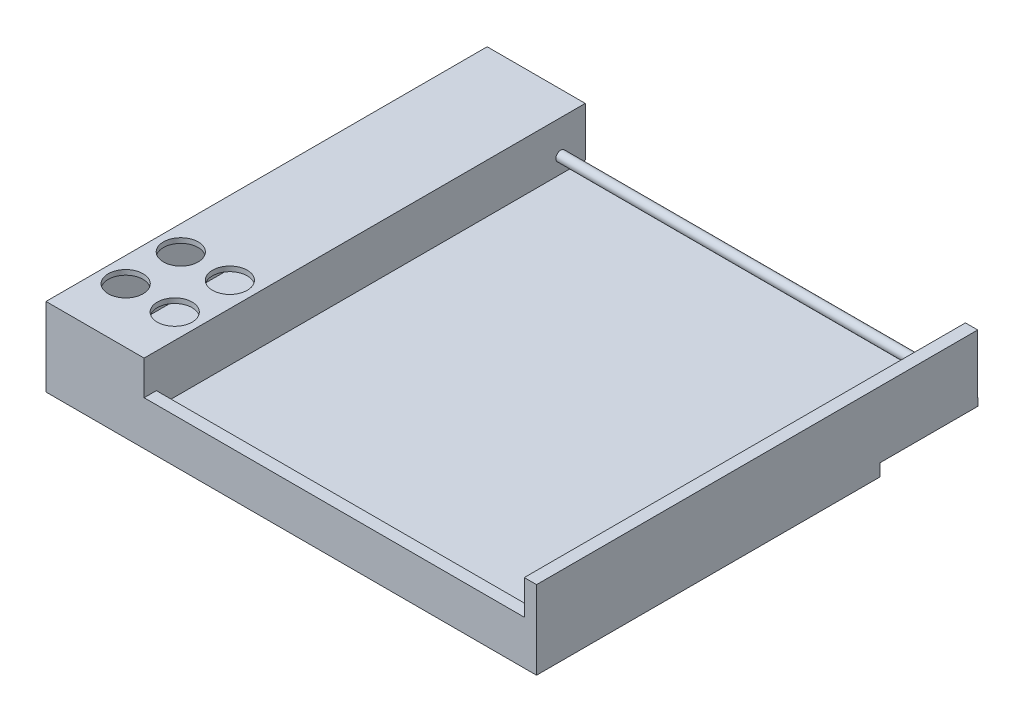
SolidWorks part; units mm, degrees
ref_plane "Front Plane" through (0, 0, 0) normal (0, 0, 1) x (1, 0, 0)
ref_plane "Top Plane" through (0, 0, 0) normal (0, 1, 0) x (1, 0, 0)
ref_plane "Right Plane" through (0, 0, 0) normal (1, 0, 0) x (0, 0, -1)
sketch "Sketch1" plane through (0, 0, 0) normal (0, 1, 0) x (1, 0, 0)
  line L1 (-100, -90) -> (100, -90)
  line L2 (-100, -90) -> (-100, 90)
  line L3 (-100, 90) -> (100, 90)
  line L4 (100, -90) -> (100, 90)
  line L5 (-100, -90) -> (100, 90) construction
  line L6 (-100, 90) -> (100, -90) construction
  point P0 (0, 0)
  dimension "D1" = 200
  dimension "D2" = 180
extrude "Boss-Extrude1" add sketch "Sketch1" along normal blind 3
sketch "Sketch2" plane through (0, 0, 0) normal (0, -1, 0) x (1, 0, 0)
  line L0 (-100, 90) -> (100, 90)
  line L1 (-100, 90) -> (-100, -50)
  line L2 (100, 90) -> (100, -50)
  line L3 (-100, -50) -> (100, -50)
  dimension "D1" = 140
extrude "Boss-Extrude2" add sketch "Sketch2" along normal blind 5
sketch "Sketch6" plane through (0, 3, 0) normal (0, 1, 0) x (1, 0, 0)
  line L0 (-100, -90) -> (100, -90)
  line L1 (-100, -90) -> (-100, 89.8697)
  line L2 (100, -90) -> (100, 89.8697)
  line L3 (-100, 89.8697) -> (100, 89.8697)
extrude "Boss-Extrude3" add sketch "Sketch6" along normal blind 24
sketch "Sketch7" plane through (0, 0, -89.8697) normal (0, 0, -1) x (-1, 0, 0)
  line L0 (-100, 15) -> (100, 15) construction
  line L1 (-100, 27) -> (-100, 3) construction
  line L2 (100, 27) -> (100, 3) construction
  line L3 (-100, 27) -> (100, 27) construction
  line L4 (-95, 3) -> (60, 3)
  line L5 (-95, 3) -> (-95, 27)
  line L6 (-95, 27) -> (60, 27)
  line L7 (60, 3) -> (60, 27)
  line L8 (-95, 3) -> (60, 27) construction
  line L9 (-95, 27) -> (60, 3) construction
  point P6 (-17.5, 15)
  dimension "D1" = 155
  dimension "D2" = 5
extrude "Cut-Extrude1" cut sketch "Sketch7" against normal up to surface (179.8697 mm away) up to face at (0, 11, 90)
sketch "Sketch8" plane through (95, 0, 0) normal (-1, 0, 0) x (0, 0, 1)
  line L0 (90, 3) -> (-89.8697, 3) construction
  line L1 (-89.8697, 27) -> (-89.8697, 3) construction
  circle A0 centre (-79.8697, 13.5) radius 2
  dimension "D3" = 4
  dimension "D1" = 10.5
  dimension "D2" = 10
extrude "Boss-Extrude4" add sketch "Sketch8" along normal up to surface (155 mm away) up to face at (-60, 15, 0.0651)
sketch "Sketch9" plane through (0, 3, 0) normal (0, 1, 0) x (1, 0, 0)
  line L0 (95, -90) -> (95, 89.8697) construction
  line L1 (-60, -90) -> (95, -90)
  line L2 (-60, -90) -> (-60, -85)
  line L3 (-60, -85) -> (95, -85)
  line L4 (95, -90) -> (95, -85)
  dimension "D1" = 5
extrude "Boss-Extrude5" add sketch "Sketch9" along normal blind 10
sketch "Sketch11" plane through (0, 0, -89.8697) normal (0, 0, -1) x (-1, 0, 0)
  line L0 (60, 3) -> (98, 3)
  line L1 (60, 3) -> (100, 3) construction
  line L2 (98, 3) -> (98, 25)
  line L3 (98, 25) -> (62, 25)
  line L4 (62, 25) -> (62, 7)
  line L5 (62, 7) -> (60, 7)
  line L6 (60, 3) -> (60, 27) construction
  line L7 (60, 7) -> (60, 3)
  line L8 (60, 27) -> (100, 27) construction
  line L9 (100, 27) -> (100, 3) construction
  dimension "D1" = 4
  dimension "D2" = 2
  dimension "D3" = 2
  dimension "D4" = 2
extrude "Cut-Extrude3" cut sketch "Sketch11" against normal offset from surface (174.8697 mm away) 5 up to face at (8.75, 15.5, 90)
sketch "Sketch12" plane through (0, 27, 0) normal (0, 1, 0) x (1, 0, 0)
  line L0 (-80, 89.8697) -> (-80, -90) construction
  line L1 (-60, 89.8697) -> (-100, 89.8697) construction
  line L2 (-100, -90) -> (-60, -90) construction
  line L3 (-100, -0.0651) -> (-60, -0.0651) construction
  line L4 (-100, 89.8697) -> (-100, -90) construction
  line L5 (-60, -90) -> (-60, 89.8697) construction
  line L6 (-60, -0.0651) -> (-100, -90) construction
  line L7 (-100, -0.0651) -> (-60, -90) construction
  line L8 (-80, -45.0326) -> (-100, -45.0326) construction
  line L9 (-80, -45.0326) -> (-60, -45.0326) construction
  circle A0 centre (-70, -45.0326) radius 7.1
  circle A1 centre (-70, -67.5163) radius 7.1
  circle A2 centre (-90, -67.5163) radius 7.1
  circle A3 centre (-90, -45.0326) radius 7.1
  point P12 (-80, -45.0326)
  dimension "D1" = 14.2
extrude "Cut-Extrude4" cut sketch "Sketch12" against normal up to surface (2 mm away) up to face at (-80, 25, -2.4349)
